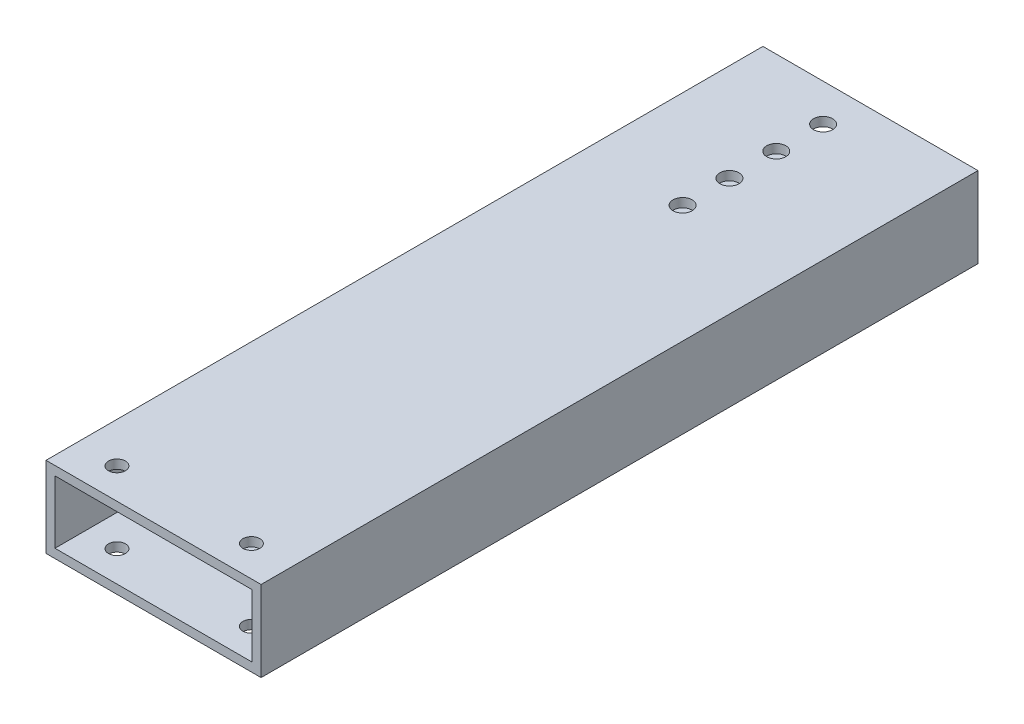
SolidWorks part; units mm, degrees
material "6061 Alloy"
ref_plane "Front Plane" through (0, 0, 0) normal (0, 0, 1) x (1, 0, 0)
ref_plane "Top Plane" through (0, 0, 0) normal (0, 1, 0) x (1, 0, 0)
ref_plane "Right Plane" through (0, 0, 0) normal (1, 0, 0) x (0, 0, -1)
sketch "Sketch1" plane through (0, 0, 0) normal (0, 1, 0) x (1, 0, 0)
  line L1 (0, 0) -> (76.2, 0)
  line L2 (0, 0) -> (0, 254)
  line L3 (0, 254) -> (76.2, 254)
  line L4 (76.2, 0) -> (76.2, 254)
  dimension "D1" = 254
  dimension "D2" = 76.2
extrude "Boss-Extrude1" add sketch "Sketch1" along normal blind 3.175
ref_plane "Plane1" through (38.1, 0, 0) normal (-1, 0, 0) x (0, 0, 1)
sketch "Sketch2" plane through (0, 3.175, 0) normal (0, 1, 0) x (1, 0, 0)
  line L0 (0, 0) -> (76.2, 0) construction
  line L1 (0, 254) -> (3.175, 254)
  line L2 (0, 254) -> (0, 0)
  line L3 (0, 0) -> (3.175, 0)
  line L4 (3.175, 254) -> (3.175, 0)
  line L5 (76.2, 254) -> (0, 254) construction
  line L6 (76.2, 0) -> (73.025, 0)
  line L7 (76.2, 0) -> (76.2, 254)
  line L8 (76.2, 254) -> (73.025, 254)
  line L9 (73.025, 0) -> (73.025, 254)
  dimension "D1" = 3.175
  dimension "D2" = 3.175
extrude "Boss-Extrude2" add sketch "Sketch2" along normal blind 25.4
sketch "Sketch3" plane through (3.175, 0, 0) normal (1, 0, 0) x (0, 0, -1)
  line L0 (254, 28.575) -> (254, 3.175) construction
  line L1 (0, 28.575) -> (254, 28.575)
  line L2 (0, 28.575) -> (0, 25.4)
  line L3 (0, 25.4) -> (254, 25.4)
  line L4 (254, 28.575) -> (254, 25.4)
  dimension "D1" = 3.175
extrude "Boss-Extrude3" add sketch "Sketch3" along normal up to next
sketch "Sketch4" plane through (0, 0, 0) normal (0, -1, 0) x (1, 0, 0)
  circle A0 centre (34.5313, -191.0131) radius 3.3782
  circle A1 centre (34.5313, -207.6044) radius 3.3782
  circle A2 centre (34.5313, -224.1956) radius 3.3782
  circle A3 centre (34.5313, -240.7869) radius 3.3782
  dimension "D1" = 6.7564
  dimension "D2" = 6.7564
  dimension "D3" = 6.7564
  dimension "D4" = 6.7564
extrude "Cut-Extrude1" cut sketch "Sketch4" against normal through all
sketch "Sketch5" plane through (0, 28.575, 0) normal (0, 1, 0) x (1, 0, 0)
  circle A0 centre (14.2875, 10.8526) radius 3
  circle A1 centre (61.9125, 10.8526) radius 3
  dimension "D1" = 6
  dimension "D2" = 6
extrude "Cut-Extrude2" cut sketch "Sketch5" against normal through all
